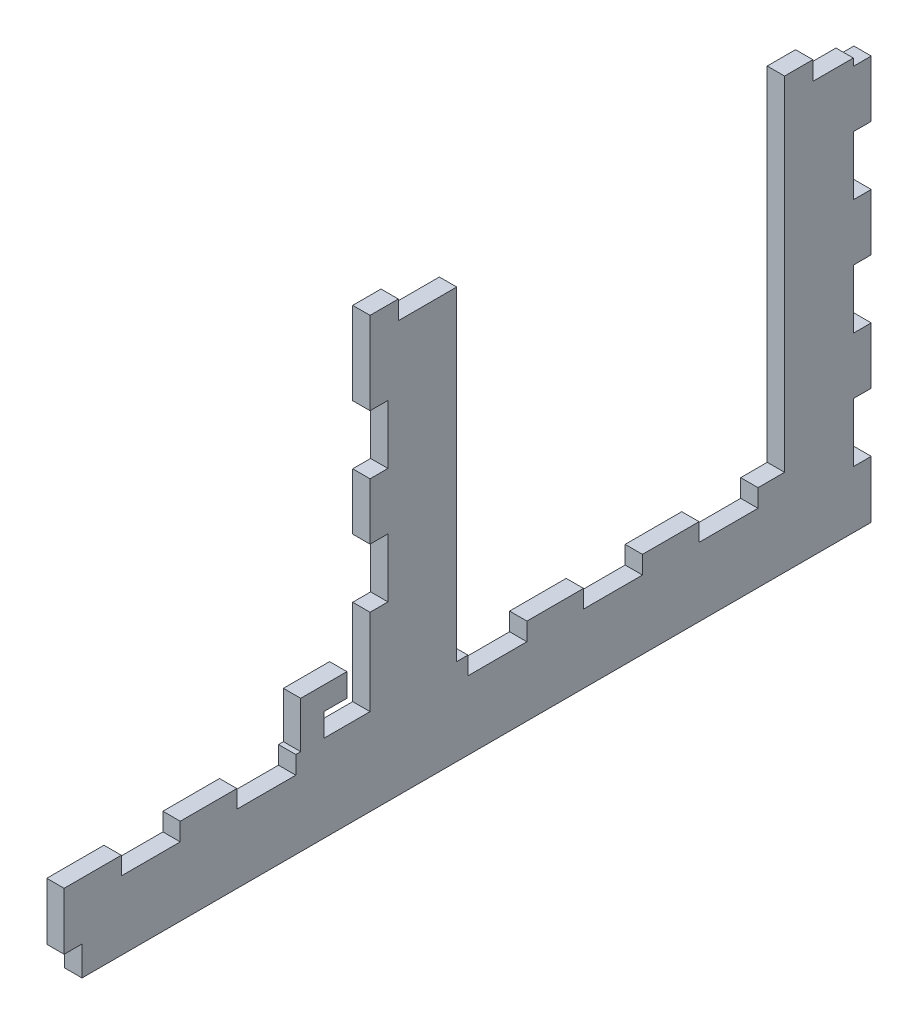
SolidWorks part; units mm, degrees
ref_plane "Front Plane" through (0, 0, 0) normal (0, 0, 1) x (1, 0, 0)
ref_plane "Top Plane" through (0, 0, 0) normal (0, 1, 0) x (1, 0, 0)
ref_plane "Right Plane" through (0, 0, 0) normal (1, 0, 0) x (0, 0, -1)
sketch "Sketch1" plane through (0, 0, 0) normal (0, 1, 0) x (1, 0, 0)
  line L0 (0, 0) -> (0, 103.7444) construction
  line L1 (-34.8722, 0) -> (34.8722, 0) construction
  line L2 (-34.8722, 0) -> (-34.8722, 103.7444) construction
  line L3 (34.8722, 103.7444) -> (34.8722, 0) construction
  line L4 (34.8722, 0) -> (34.8722, 103.7444) construction
  line L7 (-24.9087, 103.7444) -> (-24.9087, 0) construction
  line L8 (24.9087, 103.7444) -> (24.9087, 0) construction
  line L9 (31.8722, 103.7444) -> (31.8722, 0) construction
  line L10 (51.8722, 103.7444) -> (-51.8722, 103.7444) construction
  line L11 (51.8722, 100.7444) -> (-51.8722, 100.7444) construction
  line L13 (51.8722, 88.7444) -> (-51.8722, 88.7444) construction
  line L14 (-51.8722, 20) -> (51.8722, 20) construction
  line L15 (51.8722, 17) -> (-51.8722, 17) construction
  line L16 (-24.9087, 103.7444) -> (-24.9087, 0) construction
  line L17 (24.9087, 103.7444) -> (24.9087, 0) construction
  line L19 (31.8722, 103.7444) -> (31.8722, 0) construction
  line L20 (34.8722, 103.7444) -> (-34.8722, 103.7444) construction
  line L21 (51.8722, 100.7444) -> (-51.8722, 100.7444) construction
  line L24 (51.8722, 88.7444) -> (-51.8722, 88.7444) construction
  line L25 (-51.8722, 20) -> (51.8722, 20) construction
  line L26 (51.8722, 17) -> (-51.8722, 17) construction
  line L27 (31.8722, 93.7444) -> (34.8722, 93.7444) construction
  line L28 (31.8722, 93.7444) -> (34.8722, 93.7444) construction
ref_plane "Plane1" through (34.8722, 0, 0) normal (1, 0, 0) x (0, 0, -1)
sketch "Sketch2" plane through (34.8722, 0, 0) normal (1, 0, 0) x (0, 0, -1)
  line L0 (103.7444, 3) -> (103.7444, -72)
  line L1 (103.7444, -72) -> (-35.95, -72)
  line L2 (17, -57) -> (17, 3)
  line L7 (32, -57) -> (88.7444, -57)
  line L10 (93.7444, 0) -> (93.7444, 3) construction
  line L11 (93.7444, 3) -> (103.7444, 3) construction
  line L13 (93.7444, 0) -> (103.7444, 0) construction
  line L15 (-35.95, -72) -> (-65.95, -72) construction
  line L18 (103.7444, -46) -> (17, -46) construction
  line L19 (-65.95, -72) -> (-65.95, -57) construction
  line L20 (-65.95, -44.7) -> (-65.95, 65.6444) construction
  line L21 (-35.95, -72) -> (-35.95, -57)
  line L22 (-35.95, -57) -> (-65.95, -57) construction
  line L23 (17, -57) -> (-35.95, -57)
  line L24 (103.7444, 3) -> (88.7444, 3)
  line L25 (88.7444, 3) -> (88.7444, -57)
  line L26 (32, -57) -> (32, 3)
  line L27 (32, 3) -> (17, 3)
  dimension "D1" = 46
  dimension "D2" = 72
  dimension "D3" = 15
  dimension "D4" = 30
extrude "Boss-Extrude1" add sketch "Sketch2" against normal up to vertex (3 mm away) up to point (31.8722, 0, -103.7444)
sketch "Sketch4" plane through (34.8722, 0, 0) normal (1, 0, 0) x (0, 0, -1)
  line L0 (88.7444, 3) -> (88.7444, -57) construction
  line L1 (32, -57) -> (88.7444, -57) construction
  line L2 (32, -57) -> (32, 3) construction
  line L3 (32, 3) -> (17, 3) construction
  line L4 (17, -57) -> (17, 3) construction
  line L5 (17, -57) -> (-35.95, -57) construction
  line L6 (-35.95, -72) -> (-35.95, -57) construction
  line L7 (103.7444, -72) -> (-35.95, -72) construction
  line L8 (103.7444, 3) -> (103.7444, -72) construction
  line L9 (103.7444, 3) -> (88.7444, 3) construction
  line L10 (88.7444, 3) -> (88.7444, -57) construction
  line L11 (32, -57) -> (88.7444, -57) construction
  line L12 (32, -57) -> (32, 3) construction
  line L13 (32, 3) -> (17, 3) construction
  line L14 (17, -57) -> (17, 3) construction
  line L15 (17, -57) -> (-35.95, -57) construction
  line L16 (-35.95, -72) -> (-35.95, -57) construction
  line L17 (103.7444, -72) -> (-35.95, -72) construction
  line L18 (103.7444, 3) -> (103.7444, -72) construction
  line L19 (103.7444, 3) -> (88.7444, 3) construction
  line L20 (100.7444, 0) -> (100.7444, -72) construction
  line L21 (100.7444, 0) -> (88.7444, 0) construction
  line L22 (100.7444, 0) -> (103.7444, 0) construction
  line L23 (100.7444, 0) -> (100.7444, 3) construction
  line L24 (-15.95, -57) -> (-25.95, -57)
  line L25 (88.7444, -57) -> (103.7444, -57) construction
  line L26 (93.7444, -0.75) -> (100.7444, -0.75)
  line L27 (103.7444, 3) -> (88.7444, 3)
  line L28 (93.7444, 2.5) -> (93.7444, -0.75)
  line L29 (103.7444, -2) -> (103.7444, 3)
  line L30 (103.7444, -12) -> (100.7444, -12)
  line L31 (103.7444, -52) -> (103.7444, -62)
  line L32 (103.7444, -22) -> (100.7444, -22)
  line L33 (100.7444, -62) -> (100.7444, -52)
  line L34 (103.7444, -32) -> (100.7444, -32)
  line L35 (100.7444, -42) -> (100.7444, -32)
  line L36 (103.7444, -42) -> (100.7444, -42)
  line L37 (103.7444, -32) -> (103.7444, -42)
  line L38 (103.7444, -52) -> (100.7444, -52)
  line L39 (100.7444, -12) -> (100.7444, -22)
  line L40 (103.7444, -62) -> (100.7444, -62)
  line L41 (103.7444, -22) -> (103.7444, -12)
  line L42 (-32.95, -60) -> (-32.95, -72) construction
  line L43 (32, -57) -> (32, -72) construction
  line L44 (29, -57) -> (29, -72) construction
  line L45 (32, -57) -> (29, -57) construction
  line L46 (103.7444, -60) -> (-32.95, -60) construction
  line L47 (-15.95, -60) -> (-25.95, -60)
  line L50 (32, -0.75) -> (22, -0.75)
  line L51 (22, 2.5) -> (22, -0.75)
  line L52 (4.05, -57) -> (4.05, -60)
  line L53 (-32.95, -60) -> (-35.95, -60) construction
  line L54 (-32.95, -60) -> (-32.95, -57) construction
  line L55 (-25.95, -58.5) -> (-35.95, -58.5) construction
  line L56 (32, -67) -> (29, -67) construction
  line L57 (32, -67) -> (32, -72) construction
  line L58 (32, -72) -> (29, -72) construction
  line L59 (29, -67) -> (29, -72) construction
  line L60 (-32.95, -67) -> (-35.95, -67)
  line L61 (-32.95, -67) -> (-32.95, -72)
  line L62 (-32.95, -72) -> (-35.95, -72)
  line L63 (-35.95, -67) -> (-35.95, -72)
  line L65 (-25.95, -57) -> (-25.95, -60)
  line L67 (-15.95, -57) -> (-15.95, -60)
  line L68 (-25.95, -58.5) -> (-15.95, -58.5) construction
  line L69 (4.05, -58.5) -> (-5.95, -58.5) construction
  line L71 (-5.95, -57) -> (-5.95, -60)
  line L72 (-35.95, -60) -> (-35.95, -57) construction
  line L73 (34.05, -58.5) -> (44.05, -58.5) construction
  line L74 (-5.95, -58.5) -> (-15.95, -58.5) construction
  line L76 (4.05, -58.5) -> (14.05, -58.5) construction
  line L77 (14.05, -58.5) -> (24.05, -58.5) construction
  line L78 (24.05, -58.5) -> (34.05, -58.5) construction
  line L80 (24.05, -60) -> (24.05, -57) construction
  line L82 (34.05, -60) -> (34.05, -57)
  line L84 (44.05, -57) -> (44.05, -60)
  line L86 (54.05, -57) -> (54.05, -60)
  line L88 (64.05, -57) -> (64.05, -60)
  line L90 (74.05, -57) -> (74.05, -60)
  line L91 (44.05, -58.5) -> (54.05, -58.5) construction
  line L92 (54.05, -58.5) -> (64.05, -58.5) construction
  line L93 (64.05, -58.5) -> (74.05, -58.5) construction
  line L94 (14.05, -57) -> (14.05, -60) construction
  line L95 (-5.95, -60) -> (4.05, -60)
  line L96 (4.05, -57) -> (-5.95, -57)
  line L97 (44.05, -57) -> (34.05, -57)
  line L98 (44.05, -60) -> (34.05, -60)
  line L99 (64.05, -57) -> (54.05, -57)
  line L100 (54.05, -60) -> (64.05, -60)
  line L101 (74.05, -58.5) -> (84.05, -58.5) construction
  line L102 (84.05, -58.5) -> (84.05, -57) construction
  line L103 (84.05, -57) -> (84.05, -60)
  line L104 (84.05, -57) -> (74.05, -57)
  line L105 (84.05, -60) -> (74.05, -60)
  line L106 (103.7444, -2) -> (100.7444, -2)
  line L107 (100.7444, -2) -> (100.7444, -0.75)
  line L108 (32, -0.75) -> (32, 3)
  line L109 (22, 2.5) -> (17, 2.5)
  line L110 (17, 2.5) -> (17, 3)
  line L111 (17, 3) -> (32, 3)
  line L112 (93.7444, 2.5) -> (88.7444, 2.5)
  line L113 (88.7444, 2.5) -> (88.7444, 3)
  line L114 (93.7444, 0) -> (103.7444, 0) construction
  line L115 (20, 3) -> (20, -72) construction
  line L116 (17, -57) -> (17, -72) construction
  line L117 (17, -57) -> (20, -57) construction
  line L119 (20, -12) -> (17, -12)
  line L120 (20, -12) -> (20, -22)
  line L121 (20, -22) -> (17, -22)
  line L122 (17, -12) -> (17, -22)
  line L123 (20, -32) -> (17, -32)
  line L124 (20, -32) -> (20, -42)
  line L125 (20, -42) -> (17, -42)
  line L126 (17, -32) -> (17, -42)
  dimension "D3" = 5
  dimension "D4" = 10
sketch "Sketch6" plane through (34.8722, 0, 0) normal (1, 0, 0) x (0, 0, -1)
  line L0 (103.8444, -31.9) -> (100.6444, -31.9)
  line L1 (100.6444, -31.9) -> (100.6444, -42.1)
  line L2 (100.6444, -42.1) -> (103.8444, -42.1)
  line L3 (103.8444, -42.1) -> (103.8444, -31.9)
  line L4 (103.7444, -32) -> (100.7444, -32)
  line L5 (100.7444, -32) -> (100.7444, -42)
  line L6 (100.7444, -42) -> (103.7444, -42)
  line L7 (103.7444, -42) -> (103.7444, -32)
  line L8 (103.7444, -32) -> (100.7444, -32) construction
  line L9 (100.7444, -32) -> (100.7444, -42) construction
  line L10 (100.7444, -42) -> (103.7444, -42) construction
  line L11 (103.7444, -42) -> (103.7444, -32) construction
  line L12 (103.7444, -62) -> (103.7444, -52)
  line L13 (100.7444, -62) -> (103.7444, -62)
  line L14 (100.7444, -52) -> (100.7444, -62)
  line L15 (103.7444, -52) -> (100.7444, -52)
  line L16 (103.7444, -62) -> (103.7444, -52) construction
  line L17 (100.7444, -62) -> (103.7444, -62) construction
  line L18 (100.7444, -52) -> (100.7444, -62) construction
  line L19 (103.7444, -52) -> (100.7444, -52) construction
  line L20 (103.7444, -12) -> (100.7444, -12)
  line L21 (100.7444, -12) -> (100.7444, -22)
  line L22 (100.7444, -22) -> (103.7444, -22)
  line L23 (103.7444, -22) -> (103.7444, -12)
  line L24 (103.7444, -12) -> (100.7444, -12) construction
  line L25 (100.7444, -12) -> (100.7444, -22) construction
  line L26 (100.7444, -22) -> (103.7444, -22) construction
  line L27 (103.7444, -22) -> (103.7444, -12) construction
  line L28 (-32.95, -67) -> (-35.95, -67)
  line L29 (-35.95, -67) -> (-35.95, -72)
  line L30 (-35.95, -72) -> (-32.95, -72)
  line L31 (-32.95, -72) -> (-32.95, -67)
  line L32 (-32.95, -67) -> (-35.95, -67) construction
  line L33 (-35.95, -67) -> (-35.95, -72) construction
  line L34 (-35.95, -72) -> (-32.95, -72) construction
  line L35 (-32.95, -72) -> (-32.95, -67) construction
  line L36 (-15.95, -57) -> (-25.95, -57)
  line L37 (-25.95, -57) -> (-25.95, -60)
  line L38 (-25.95, -60) -> (-15.95, -60)
  line L39 (-15.95, -60) -> (-15.95, -57)
  line L40 (-15.95, -57) -> (-25.95, -57) construction
  line L41 (-25.95, -57) -> (-25.95, -60) construction
  line L42 (-25.95, -60) -> (-15.95, -60) construction
  line L43 (-15.95, -60) -> (-15.95, -57) construction
  line L44 (34.05, -57) -> (34.05, -60)
  line L45 (44.05, -57) -> (34.05, -57)
  line L46 (44.05, -60) -> (44.05, -57)
  line L47 (34.05, -60) -> (44.05, -60)
  line L48 (34.05, -57) -> (34.05, -60) construction
  line L49 (44.05, -57) -> (34.05, -57) construction
  line L50 (44.05, -60) -> (44.05, -57) construction
  line L51 (34.05, -60) -> (44.05, -60) construction
  line L52 (-5.95, -57) -> (-5.95, -60)
  line L53 (4.05, -57) -> (-5.95, -57)
  line L54 (4.05, -60) -> (4.05, -57)
  line L55 (-5.95, -60) -> (4.05, -60)
  line L56 (-5.95, -57) -> (-5.95, -60) construction
  line L57 (4.05, -57) -> (-5.95, -57) construction
  line L58 (4.05, -60) -> (4.05, -57) construction
  line L59 (-5.95, -60) -> (4.05, -60) construction
  line L60 (20, -12) -> (17, -12)
  line L61 (20, -22) -> (20, -12)
  line L62 (17, -22) -> (20, -22)
  line L63 (17, -12) -> (17, -22)
  line L64 (20, -12) -> (17, -12) construction
  line L65 (20, -22) -> (20, -12) construction
  line L66 (17, -22) -> (20, -22) construction
  line L67 (17, -12) -> (17, -22) construction
  line L68 (74.05, -57) -> (74.05, -60)
  line L69 (74.05, -60) -> (84.05, -60)
  line L70 (84.05, -60) -> (84.05, -57)
  line L71 (84.05, -57) -> (74.05, -57)
  line L72 (74.05, -57) -> (74.05, -60) construction
  line L73 (74.05, -60) -> (84.05, -60) construction
  line L74 (84.05, -60) -> (84.05, -57) construction
  line L75 (84.05, -57) -> (74.05, -57) construction
  line L76 (54.05, -60) -> (64.05, -60)
  line L77 (54.05, -57) -> (54.05, -60)
  line L78 (64.05, -57) -> (54.05, -57)
  line L79 (64.05, -60) -> (64.05, -57)
  line L80 (54.05, -60) -> (64.05, -60) construction
  line L81 (54.05, -57) -> (54.05, -60) construction
  line L82 (64.05, -57) -> (54.05, -57) construction
  line L83 (64.05, -60) -> (64.05, -57) construction
  line L84 (20, -32) -> (17, -32)
  line L85 (20, -42) -> (20, -32)
  line L86 (17, 2.5) -> (22, 2.5)
  line L87 (22, 2.5) -> (22, -0.75)
  line L88 (22, -0.75) -> (32, -0.75)
  line L89 (32, -0.75) -> (32, 3)
  line L90 (32, 3) -> (17, 3)
  line L91 (17, 3) -> (17, 2.5)
  line L92 (17, 2.5) -> (22, 2.5) construction
  line L93 (22, 2.5) -> (22, -0.75) construction
  line L94 (22, -0.75) -> (32, -0.75) construction
  line L95 (32, -0.75) -> (32, 3) construction
  line L96 (32, 3) -> (17, 3) construction
  line L97 (17, 3) -> (17, 2.5) construction
  line L98 (17, -42) -> (20, -42)
  line L99 (17, -32) -> (17, -42)
  line L100 (93.7444, -0.75) -> (100.7444, -0.75)
  line L101 (93.7444, 2.5) -> (93.7444, -0.75)
  line L102 (88.7444, 2.5) -> (93.7444, 2.5)
  line L103 (88.7444, 3) -> (88.7444, 2.5)
  line L104 (103.7444, 3) -> (88.7444, 3)
  line L105 (103.7444, -2) -> (103.7444, 3)
  line L106 (100.7444, -2) -> (103.7444, -2)
  line L107 (100.7444, -0.75) -> (100.7444, -2)
  line L108 (93.7444, -0.75) -> (100.7444, -0.75) construction
  line L109 (93.7444, 2.5) -> (93.7444, -0.75) construction
  line L110 (88.7444, 2.5) -> (93.7444, 2.5) construction
  line L111 (88.7444, 3) -> (88.7444, 2.5) construction
  line L112 (103.7444, 3) -> (88.7444, 3) construction
  line L113 (103.7444, -2) -> (103.7444, 3) construction
  line L114 (100.7444, -2) -> (103.7444, -2) construction
  line L115 (100.7444, -0.75) -> (100.7444, -2) construction
  line L116 (20, -32) -> (17, -32) construction
  line L117 (20, -42) -> (20, -32) construction
  line L118 (17, -42) -> (20, -42) construction
  line L119 (17, -32) -> (17, -42) construction
  line L120 (103.8444, -62.1) -> (103.8444, -51.9)
  line L121 (103.8444, -51.9) -> (100.6444, -51.9)
  line L122 (100.6444, -51.9) -> (100.6444, -62.1)
  line L123 (100.6444, -62.1) -> (103.8444, -62.1)
  line L124 (103.8444, -11.9) -> (100.6444, -11.9)
  line L125 (100.6444, -11.9) -> (100.6444, -22.1)
  line L126 (100.6444, -22.1) -> (103.8444, -22.1)
  line L127 (103.8444, -22.1) -> (103.8444, -11.9)
  line L128 (-32.85, -66.9) -> (-36.05, -66.9)
  line L129 (-36.05, -66.9) -> (-36.05, -72.1)
  line L130 (-36.05, -72.1) -> (-32.85, -72.1)
  line L131 (-32.85, -72.1) -> (-32.85, -66.9)
  line L132 (-15.85, -56.9) -> (-26.05, -56.9)
  line L133 (-26.05, -56.9) -> (-26.05, -60.1)
  line L134 (-26.05, -60.1) -> (-15.85, -60.1)
  line L135 (-15.85, -60.1) -> (-15.85, -56.9)
  line L136 (33.95, -56.9) -> (33.95, -60.1)
  line L137 (33.95, -60.1) -> (44.15, -60.1)
  line L138 (44.15, -60.1) -> (44.15, -56.9)
  line L139 (44.15, -56.9) -> (33.95, -56.9)
  line L140 (-6.05, -56.9) -> (-6.05, -60.1)
  line L141 (-6.05, -60.1) -> (4.15, -60.1)
  line L142 (4.15, -60.1) -> (4.15, -56.9)
  line L143 (4.15, -56.9) -> (-6.05, -56.9)
  line L144 (20.1, -11.9) -> (16.9, -11.9)
  line L145 (16.9, -11.9) -> (16.9, -22.1)
  line L146 (16.9, -22.1) -> (20.1, -22.1)
  line L147 (20.1, -22.1) -> (20.1, -11.9)
  line L148 (73.95, -56.9) -> (73.95, -60.1)
  line L149 (73.95, -60.1) -> (84.15, -60.1)
  line L150 (84.15, -60.1) -> (84.15, -56.9)
  line L151 (84.15, -56.9) -> (73.95, -56.9)
  line L152 (53.95, -60.1) -> (64.15, -60.1)
  line L153 (64.15, -60.1) -> (64.15, -56.9)
  line L154 (64.15, -56.9) -> (53.95, -56.9)
  line L155 (53.95, -56.9) -> (53.95, -60.1)
  line L156 (16.9, 2.4) -> (21.9, 2.4)
  line L157 (21.9, 2.4) -> (21.9, -0.85)
  line L158 (21.9, -0.85) -> (32.1, -0.85)
  line L159 (32.1, -0.85) -> (32.1, 3.1)
  line L160 (32.1, 3.1) -> (16.9, 3.1)
  line L161 (16.9, 3.1) -> (16.9, 2.4)
  line L162 (93.6444, -0.85) -> (100.6444, -0.85)
  line L163 (100.6444, -0.85) -> (100.6444, -2.1)
  line L164 (100.6444, -2.1) -> (103.8444, -2.1)
  line L165 (103.8444, -2.1) -> (103.8444, 3.1)
  line L166 (103.8444, 3.1) -> (88.6444, 3.1)
  line L167 (88.6444, 3.1) -> (88.6444, 2.4)
  line L168 (88.6444, 2.4) -> (93.6444, 2.4)
  line L169 (93.6444, 2.4) -> (93.6444, -0.85)
  line L170 (20.1, -31.9) -> (16.9, -31.9)
  line L171 (16.9, -31.9) -> (16.9, -42.1)
  line L172 (16.9, -42.1) -> (20.1, -42.1)
  line L173 (20.1, -42.1) -> (20.1, -31.9)
  dimension "D1" = 0
  dimension "D2" = 0
  dimension "D3" = 0
  dimension "D4" = 0
  dimension "D5" = 0
  dimension "D6" = 0
  dimension "D7" = 0
  dimension "D8" = 0
  dimension "D9" = 0
  dimension "D10" = 0
  dimension "D11" = 0
  dimension "D12" = 0
  dimension "D13" = 0
  dimension "D14" = 0.1
extrude "Cut-Extrude1" cut sketch "Sketch6" against normal through all
sketch "Sketch8" plane through (34.8722, 0, 0) normal (1, 0, 0) x (0, 0, -1)
  line L0 (13, -53) -> (13, -49)
  line L1 (17, -57) -> (5, -57) construction
  line L2 (17, -57) -> (17, -49) construction
  line L3 (17, -49) -> (5, -49) construction
  line L4 (5, -57) -> (5, -49) construction
  line L5 (13, -49) -> (5, -49)
  line L6 (5, -49) -> (5, -57)
  line L7 (5, -57) -> (9, -57)
  line L8 (9, -57) -> (9, -53)
  line L9 (9, -53) -> (13, -53)
  line L10 (9, -53) -> (5, -53) construction
  line L11 (13, -53) -> (17, -53) construction
  line L12 (13, -53) -> (13, -57) construction
  dimension "D1" = 4
extrude "Boss-Extrude2" add sketch "Sketch8" against normal up to surface (3 mm away) up to face at (31.8722, -40.2552, -47.8188)
